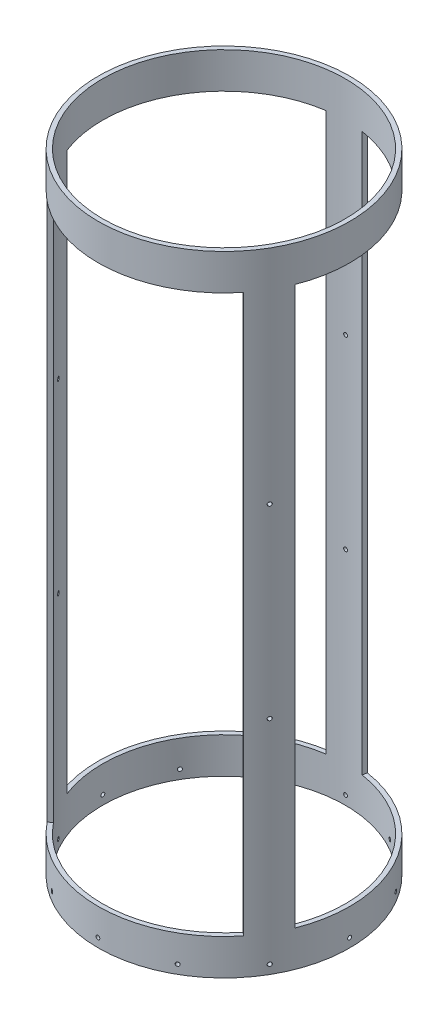
SolidWorks part; units mm, degrees
material "6061-T6 (SS)"
ref_plane "Front Plane" through (0, 0, 0) normal (0, 0, 1) x (1, 0, 0)
ref_plane "Top Plane" through (0, 0, 0) normal (0, 1, 0) x (1, 0, 0)
ref_plane "Right Plane" through (0, 0, 0) normal (1, 0, 0) x (0, 0, -1)
sketch "Sketch1" plane through (0, 0, 0) normal (0, 1, 0) x (1, 0, 0)
  circle A0 centre (0, 0) radius 88.9
  circle A1 centre (0, 0) radius 85.725
  dimension "D1" = 177.8
  dimension "D2" = 171.45
extrude "Boss-Extrude1" add sketch "Sketch1" along normal mid plane 444.5
sketch "Sketch6" plane through (0, -222.25, 0) normal (0, -1, 0) x (-1, 0, 0)
  line L0 (82.7901, -32.3885) -> (79.8333, -31.2317)
  line L1 (13.1222, 87.9262) -> (12.6536, 84.786)
  line L2 (0, 0) -> (0, 85.725) construction
  line L3 (-97.8543, 0) -> (97.8543, 0) construction
  line L4 (0, 0) -> (12.6536, 84.786) construction
  arc A0 (13.1222, 87.9262) -> (82.7901, -32.3885) centre (0, 0) cw
  circle A1 centre (0, 0) radius 88.9 construction
  arc A2 (12.6536, 84.786) -> (79.8333, -31.2317) centre (0, 0) cw
  circle A3 centre (0, 0) radius 85.725 construction
  arc A4 (0, 85.725) -> (12.6536, 84.786) centre (0, 0) cw construction
  dimension "D1" = 153.924
  dimension "D2" = 12.7
extrude "Cut-Extrude5" cut sketch "Sketch6" against normal offset from surface (393.7 mm away) 25.4 from offset 25.4 up to face at (0, 222.25, 88.9) offset against normal yes
pattern_circular "CirPattern5" count 3 over 360 about axis through (0, 0, 0) along (0, 1, 0) of "Cut-Extrude5"
ref_plane "Plane1" through (0, 0, -88.9) normal (0, 0, -1) x (-1, 0, 0)
sketch "Sketch3" plane through (0, 0, 0) normal (0, 0, -1) x (-1, 0, 0)
  line L1 (-88.9, -222.25) -> (88.9, -222.25) construction
  line L3 (-12.8692, 196.85) -> (-12.8692, -196.85) construction
  circle A0 centre (-0.1692, -215.9) radius 1.3525
  dimension "D1" = 6.35
  dimension "D2" = 2.7051
  dimension "D4" = 12.7
extrude "Cut-Extrude2" cut sketch "Sketch3" along normal up to surface (88.8921 mm away)
pattern_circular "CirPattern2" count 12 over 360 about axis through (0, 222.25, 0) along (0, -1, 0) of "Cut-Extrude2"
sketch "Sketch4" plane through (0, 0, -88.9) normal (0, 0, -1) x (-1, 0, 0)
  line L1 (88.9, 222.25) -> (-88.9, 222.25) construction
  circle A0 centre (-0.1692, 215.9) radius 1.3525
  dimension "D1" = 2.7051
  dimension "D2" = 6.35
ref_plane "Plane2" through (0, 0, 88.9) normal (0, 0, 1) x (1, 0, 0)
sketch "Sketch5" plane through (0, 0, 88.9) normal (0, 0, 1) x (1, 0, 0)
  line L0 (-88.9, 196.85) -> (-13.1222, 196.85) construction
  line L1 (88.9, -196.85) -> (13.3458, -196.85) construction
  circle A0 centre (0.1692, 65.6167) radius 1.3526
  circle A1 centre (0.1692, -65.6167) radius 1.3526
  dimension "D1" = 131.2333
  dimension "D2" = 131.2333
  dimension "D3" = 2.7051
  dimension "D4" = 2.7051
extrude "Cut-Extrude4" cut sketch "Sketch5" against normal up to surface (177.787 mm away)
pattern_circular "CirPattern4" count 3 over 360 about axis through (0, 222.25, 0) along (0, -1, 0) of "Cut-Extrude4"
